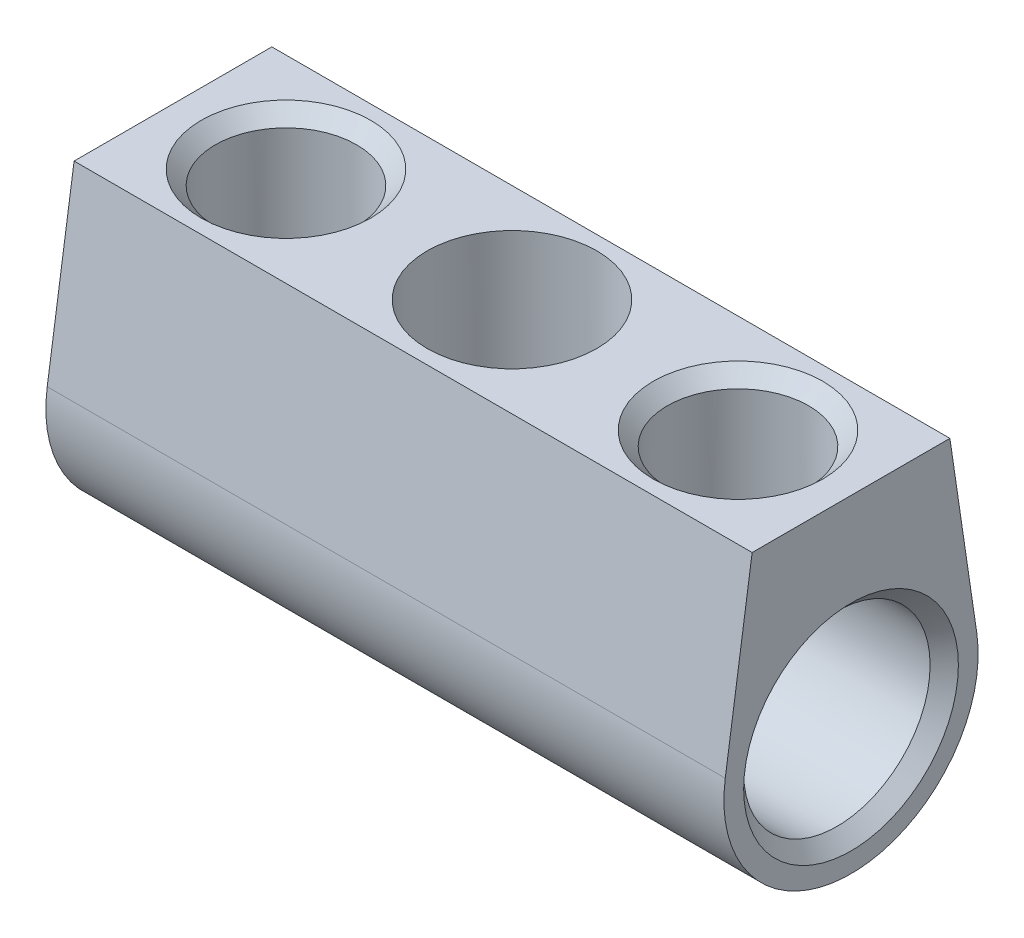
SolidWorks part; units mm, degrees
material "Brass"
ref_plane "Front Plane" through (0, 0, 0) normal (0, 0, 1) x (1, 0, 0)
ref_plane "Top Plane" through (0, 0, 0) normal (0, 1, 0) x (1, 0, 0)
ref_plane "Right Plane" through (0, 0, 0) normal (1, 0, 0) x (0, 0, -1)
sketch "Sketch1" plane through (0, 0, 0) normal (1, 0, 0) x (0, 0, -1)
  line L0 (-2.2258, 0.3288) -> (-1.75, 3.55)
  line L1 (-1.75, 3.55) -> (1.75, 3.55)
  line L2 (1.75, 3.55) -> (2.2258, 0.3288)
  line L3 (0, 0) -> (0, 3.55) construction
  circle A0 centre (0, 0) radius 1.65
  arc A1 (-2.2258, 0.3288) -> (2.2258, 0.3288) centre (0, 0) ccw
  dimension "D1" = 2.25
  dimension "D2" = 3.3
  dimension "D3" = 3.55
  dimension "D4" = 3.5
extrude "Extrude1" add sketch "Sketch1" along normal mid plane 12
sketch "Sketch2" plane through (0, 0, 0) normal (0, 1, 0) x (1, 0, 0)
  line L0 (-4, 0) -> (4, 0) construction
  circle A0 centre (-4, 0) radius 1.25
  circle A1 centre (4, 0) radius 1.25
  dimension "D1" = 2.5
  dimension "D2" = 8
extrude "Cut-Extrude1" cut sketch "Sketch2" along normal through all
cosmetic thread "Cosmetic Thread1" parameters "D2"=3
cosmetic thread "Cosmetic Thread2" parameters "D2"=3
sketch "Sketch3" plane through (0, 0, 0) normal (0, 1, 0) x (1, 0, 0)
  circle A0 centre (0, 0) radius 1.5
  dimension "D1" = 3
extrude "Cut-Extrude2" cut sketch "Sketch3" against normal through all and the other way through all
chamfer "Chamfer1" distance 0.25 angle 45 4 edges at (6, 0, -1.65) (-6, 0, -1.65) (4, 3.55, 1.25) (-4, 3.55, 1.25)
